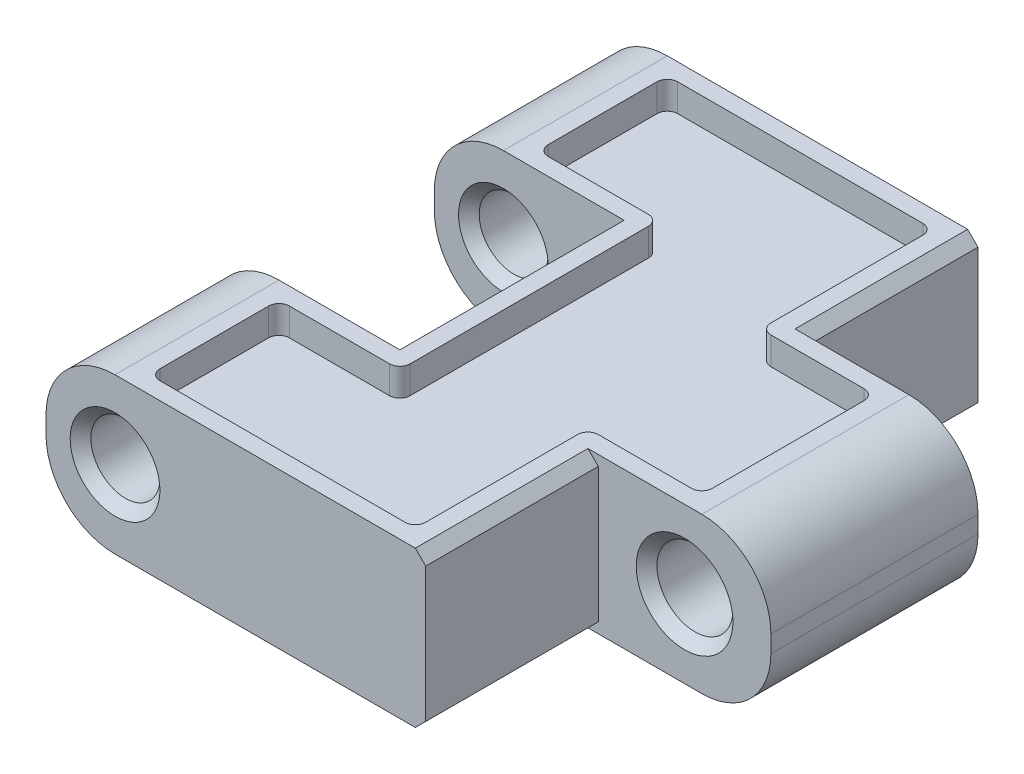
SolidWorks part; units mm, degrees
ref_plane "Ebene vorne" through (0, 0, 0) normal (0, 0, 1) x (1, 0, 0)
ref_plane "Ebene oben" through (0, 0, 0) normal (0, 1, 0) x (1, 0, 0)
ref_plane "Ebene rechts" through (0, 0, 0) normal (1, 0, 0) x (0, 0, -1)
sketch "Skizze1" plane through (0, 0, 0) normal (0, 1, 0) x (1, 0, 0)
  line L0 (0, 0) -> (16, 0) construction
  line L1 (5.5, 3.25) -> (5.5, -3.25)
  line L2 (5.5, -3.25) -> (0, -3.25)
  line L3 (0, -3.25) -> (0, -8)
  line L4 (0, -8) -> (11, -8)
  line L5 (11, -8) -> (11, -3)
  line L6 (11, -3) -> (16, -3)
  line L7 (16, -3) -> (16, 3)
  line L8 (11, 3) -> (16, 3)
  line L9 (11, 8) -> (11, 3)
  line L10 (0, 8) -> (11, 8)
  line L11 (0, 3.25) -> (0, 8)
  line L12 (5.5, 3.25) -> (0, 3.25)
  point P16 (5.5, 0)
  dimension "D1" = 16
  dimension "D2" = 5
  dimension "D3" = 5.5
  dimension "D4" = 16
  dimension "D5" = 6
  dimension "D6" = 6.5
extrude "Grundkörper" add sketch "Skizze1" along normal blind 4.5
sketch "Skizze2" plane through (0, 0, 0) normal (0, 0, 1) x (1, 0, 0)
  line L0 (0, 2.25) -> (2, 2.25) construction
  line L1 (0, 4.5) -> (0, 0) construction
  line L2 (2, 2.25) -> (13.5, 2.25) construction
  line L3 (13.5, 2.25) -> (16, 2.25) construction
  line L4 (16, 4.5) -> (16, 0) construction
  circle A0 centre (2, 2.25) radius 1
  circle A1 centre (13.5, 2.25) radius 1.1
  dimension "D3" = 2.2
  dimension "D4" = 2
  dimension "D1" = 2.5
  dimension "D2" = 2
extrude "Achsbohhrungen" cut sketch "Skizze2" against normal through all and the other way through all
sketch "Skizze3" plane through (0, 0, 0) normal (0, -1, 0) x (1, 0, 0)
  line L1 (5.5, 3.25) -> (7.5, 3.25)
  line L2 (5.5, 3.25) -> (5.5, -3.25)
  line L3 (5.5, -3.25) -> (7.5, -3.25)
  line L4 (7.5, 3.25) -> (7.5, -3.25)
  dimension "D1" = 2
extrude "Ausschnitt Zahn" cut sketch "Skizze3" against normal offset from surface (3 mm away) 1.5 up to face at (7.25, 4.5, 0)
sketch "Skizze4" plane through (0, 4.5, 0) normal (0, 1, 0) x (1, 0, 0)
  line L0 (5.5, -3.25) -> (0, -3.25) construction
  line L1 (5, -3.25) -> (9, -3.25)
  line L2 (4, -4.25) -> (4, -7)
  line L3 (5, -8) -> (9, -8)
  line L4 (9, -3.25) -> (9, -8)
  line L5 (0, -8) -> (11, -8) construction
  line L6 (11, -8) -> (11, -3) construction
  line L7 (0, -3.25) -> (0, -8) construction
  arc A0 (5, -8) -> (4, -7) centre (5, -7) cw
  arc A1 (4, -4.25) -> (5, -3.25) centre (5, -4.25) cw
  point P16 (4, -3.25)
  dimension "D3" = 1
  dimension "D1" = 2
  dimension "D2" = 4
ref_plane "Ebene2" through (0, 6.5, 0) normal (0, 1, 0) x (1, 0, 0)
sketch "Skizze5" plane through (0, 6.5, 0) normal (0, 1, 0) x (1, 0, 0)
  line L0 (9, -3.25) -> (9, -8) construction
  line L1 (9.5, -4.625) -> (6.3, -4.625)
  line L2 (9.5, -4.625) -> (9.5, -6.625)
  line L3 (9.5, -6.625) -> (6.3, -6.625)
  line L4 (6, -4.925) -> (6, -6.325)
  line L5 (4, -4.25) -> (4, -7) construction
  line L6 (9, -5.625) -> (9.5, -5.625) construction
  arc A0 (6.3, -6.625) -> (6, -6.325) centre (6.3, -6.325) cw
  arc A1 (6, -4.925) -> (6.3, -4.625) centre (6.3, -4.925) cw
  dimension "D4" = 0.3
  dimension "D1" = 0.5
  dimension "D2" = 2
  dimension "D3" = 2
loft "LaufKralle" [suppressed] add profiles "Skizze4", "Skizze5"
fillet "Verrundung7" [suppressed] radius 0.5
mirror "Spiegeln1" [suppressed] about plane through (0, 0, 0) normal (0, 0, 1)
fillet "Verrundung2" radius 2 6 edges at (0, 0, 5.625) (0, 0, -5.625) (0, 4.5, -5.625) (0, 4.5, 5.625) (16, 0, 0) (16, 4.5, 0)
chamfer "Fase1" distance 0.3 angle 45 4 edges at (11, 0, 5.5) (11, 0, -5.5) (11, 4.5, 5.5) (11, 4.5, -5.5)
chamfer "Fase2" distance 0.3 angle 45 6 edges at (14.6, 2.25, -3) (12.4, 2.25, 3) (1, 2.25, -3.25) (3, 2.25, 3.25) (3, 2.25, 8) (3, 2.25, -8)
ref_plane "Mitte" through (0, 0, 0) normal (0, 0, -1) x (-1, 0, 0)
sketch "Skizze6" plane through (0, 4.5, 0) normal (0, 1, 0) x (1, 0, 0)
  line L90 (13.5, -2.5) -> (13.5, 2.5)
  line L91 (10.2, -2.5) -> (13.5, -2.5)
  line L92 (13.5, 2.5) -> (10.2, 2.5)
  line L93 (10.2, 2.5) -> (10.2, 7.5)
  line L94 (10.2, -7.5) -> (10.2, -2.5)
  line L95 (2.5, -7.5) -> (10.2, -7.5)
  line L96 (2.5, -3.75) -> (2.5, -7.5)
  line L97 (6, -3.75) -> (2.5, -3.75)
  line L98 (6, 3.75) -> (6, -3.75)
  line L99 (2.5, 3.75) -> (6, 3.75)
  line L100 (2.5, 7.5) -> (2.5, 3.75)
  line L101 (10.2, 7.5) -> (2.5, 7.5)
  line L102 (13.5, -2.5) -> (13.5, 2.5)
  line L103 (10.2, -2.5) -> (13.5, -2.5)
  line L104 (13.5, 2.5) -> (10.2, 2.5)
  line L105 (10.2, 2.5) -> (10.2, 7.5)
  line L106 (10.2, -7.5) -> (10.2, -2.5)
  line L107 (2.5, -7.5) -> (10.2, -7.5)
  line L108 (2.5, -3.75) -> (2.5, -7.5)
  line L109 (6, -3.75) -> (2.5, -3.75)
  line L110 (6, 3.75) -> (6, -3.75)
  line L111 (2.5, 3.75) -> (6, 3.75)
  line L112 (2.5, 7.5) -> (2.5, 3.75)
  line L113 (10.2, 7.5) -> (2.5, 7.5)
  dimension "D1" = 0.5
extrude "MoosgummiVertiefung" cut sketch "Skizze6" against normal blind 0.8
fillet "Verrundung8" radius 0.3 12 edges at (10.2, 4.1, -2.5) (13.5, 4.1, -2.5) (13.5, 4.1, 2.5) (10.2, 4.1, 2.5) (10.2, 4.1, 7.5) (2.5, 4.1, 7.5) (2.5, 4.1, 3.75) (6, 4.1, 3.75) (6, 4.1, -3.75) (2.5, 4.1, -3.75) (2.5, 4.1, -7.5) (10.2, 4.1, -7.5)
equation "\"D2@Skizze2\"=\"D1@Skizze2\"-0.5"
